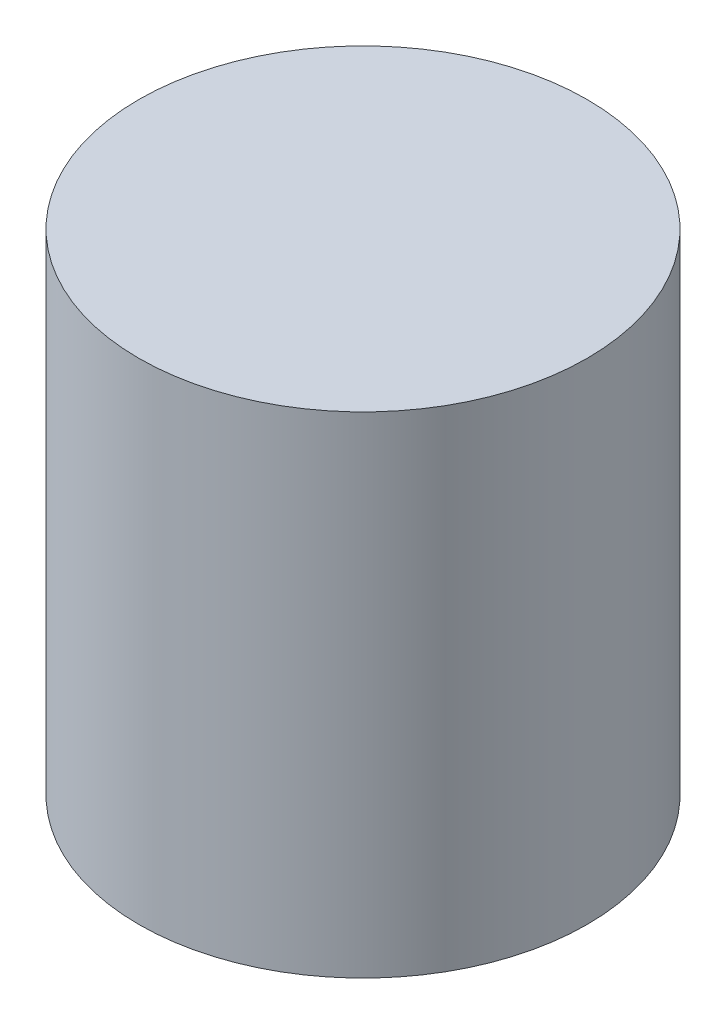
SolidWorks part; units mm, degrees
ref_plane "Спереди" through (0, 0, 0) normal (0, 0, 1) x (1, 0, 0)
ref_plane "Сверху" through (0, 0, 0) normal (0, 1, 0) x (1, 0, 0)
ref_plane "Справа" through (0, 0, 0) normal (1, 0, 0) x (0, 0, -1)
sketch "Эскиз1" plane through (0, 0, 0) normal (0, 1, 0) x (1, 0, 0)
  circle A0 centre (0, 0) radius 16
  dimension "D1" = 32
extrude "Бобышка-Вытянуть1" add sketch "Эскиз1" along normal blind 35
